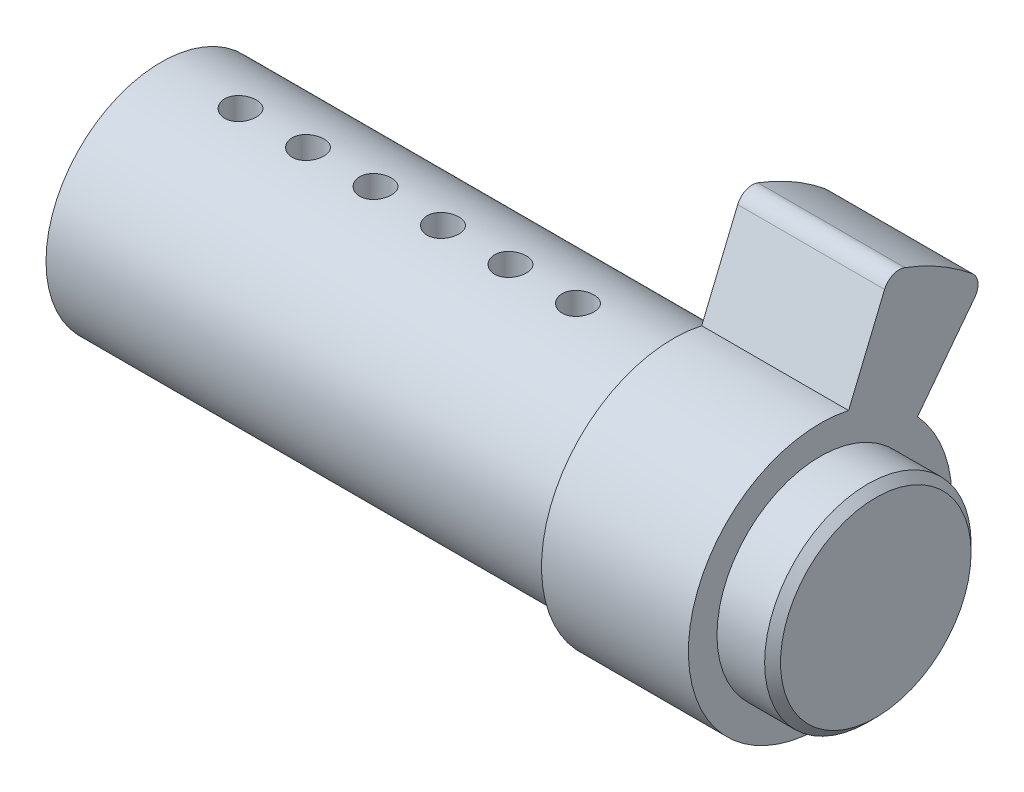
SolidWorks part; units mm, degrees
ref_plane "Front Plane" through (0, 0, 0) normal (0, 0, 1) x (1, 0, 0)
ref_plane "Top Plane" through (0, 0, 0) normal (0, 1, 0) x (1, 0, 0)
ref_plane "Right Plane" through (0, 0, 0) normal (1, 0, 0) x (0, 0, -1)
sketch "Sketch1" plane through (0, 0, 0) normal (1, 0, 0) x (0, 0, -1)
  circle A0 centre (0, 0) radius 7.25
  dimension "D1" = 14.5
extrude "outside dia" add sketch "Sketch1" along normal blind 32.25
sketch "Sketch2" plane through (0, 0, 0) normal (-1, 0, 0) x (0, 0, 1)
  line L1 (-1.25, 2) -> (1.25, 2)
  line L2 (-1.25, 2) -> (-1.25, -6.25)
  line L3 (-1.25, -6.25) -> (1.25, -6.25)
  line L4 (1.25, 2) -> (1.25, -6.25)
  line L5 (-1.25, 2) -> (1.25, -6.25) construction
  line L6 (-1.25, -6.25) -> (1.25, 2) construction
  circle A3 centre (0, 0) radius 7.25 construction
  point P0 (0, -2.125)
  dimension "D1" = 2.5
  dimension "D2" = 8.25
  dimension "D3" = 1
  dimension "D4" = 2.125
  dimension "D5" = 2
  dimension "D6" = 6.25
extrude "keyhole" cut sketch "Sketch2" against normal through all
sketch "Sketch3" plane through (0, 0, 0) normal (0, 1, 0) x (1, 0, 0)
  line L0 (0, 7.25) -> (0, -7.25) construction
  circle A0 centre (5, 0) radius 1
  dimension "D1" = 2
  dimension "D2" = 5
extrude "pin 1" cut sketch "Sketch3" along normal blind 35
pattern_linear "LPattern1" count 6 spacing 4.25 along (1, 0, 0) of "pin 1"
sketch "Sketch4" plane through (0, 0, 0) normal (0, 0, 1) x (1, 0, 0)
  line L0 (0, -3.5) -> (0, -6.25)
  line L1 (2.75, -3.5) -> (0, -6.25)
  line L2 (2.75, -3.5) -> (0, -3.5) construction
  line L3 (2.75, -3.5) -> (0, -3.5)
  dimension "D1" = 2.75
  dimension "D2" = 45
revolve "front cone 5.5 x 90 deg" cut sketch "Sketch4" angle 360 about L2
sketch "Sketch5" plane through (32.25, 0, 0) normal (1, 0, 0) x (0, 0, -1)
  line L0 (-4.15, -7.188) -> (7.55, 13.077) construction
  line L1 (0, 0) -> (0, 15.0806) construction
  line L2 (7.2168, 5.6999) -> (10.3006, 11.0412) construction
  line L3 (1.2386, 8.9453) -> (4.4116, 14.4412) construction
  line L4 (-7.0945, -5.488) -> (4.6055, 14.777) construction
  line L5 (-1.2055, -8.888) -> (10.4945, 11.377) construction
  line L6 (4.4116, 14.4412) -> (1.7872, 8.1053)
  line L7 (10.3006, 11.0412) -> (6.1258, 5.6004)
  arc A0 (1.7872, 8.1053) -> (6.1258, 5.6004) centre (0, 0) ccw
  arc A1 (4.4116, 14.4412) -> (10.3006, 11.0412) centre (0, 0) cw
  dimension "D1" = 16.6
  dimension "D2" = 23.4
  dimension "D3" = 30
  dimension "D6" = 7.5
  dimension "D7" = 7.5
  dimension "D4" = 3.4
  dimension "D5" = 3.4
extrude "cam" add sketch "Sketch5" along normal blind 9.25
fillet "R1" radius 1 2 edges at (36.875, 11.0412, -10.3006) (36.875, 14.4412, -4.4116)
sketch "Sketch6" plane through (41.5, 0, 0) normal (1, 0, 0) x (0, 0, -1)
  circle A0 centre (0, 0) radius 6.5
  dimension "D1" = 13
extrude "end bit" add sketch "Sketch6" along normal blind 3.5
chamfer "0.5 x 45 deg" distance 0.5 angle 45 1 edges at (45, 0, -6.5)
